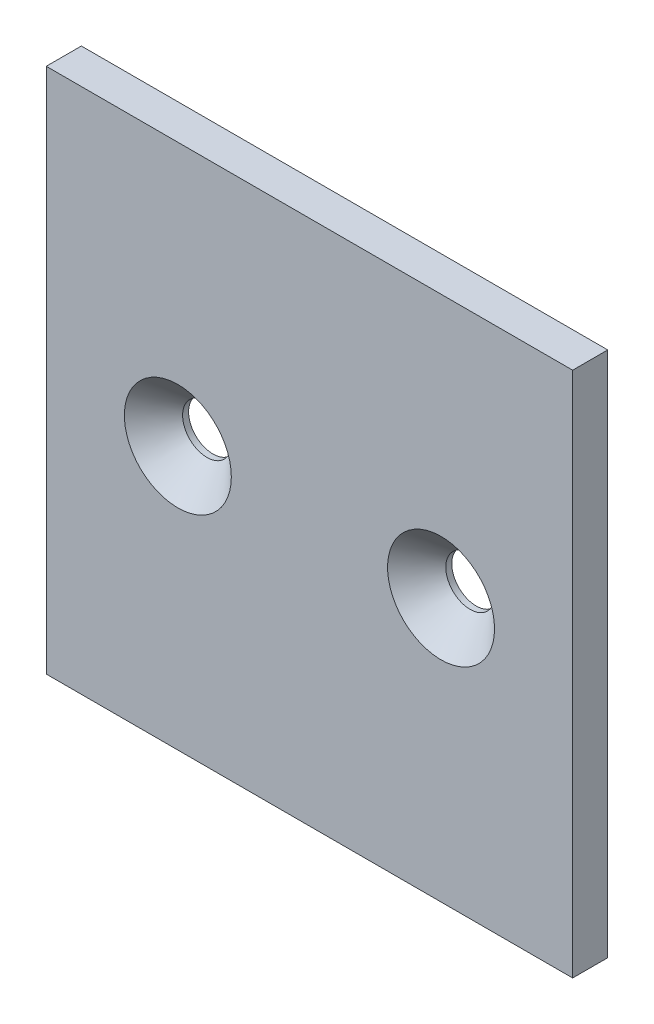
SolidWorks part; units mm, degrees
ref_plane "Front Plane" through (0, 0, 0) normal (0, 0, 1) x (1, 0, 0)
ref_plane "Top Plane" through (0, 0, 0) normal (0, 1, 0) x (1, 0, 0)
ref_plane "Right Plane" through (0, 0, 0) normal (1, 0, 0) x (0, 0, -1)
sketch "Sketch1" plane through (0, 0, 0) normal (0, 0, 1) x (1, 0, 0)
  line L0 (0, 0) -> (0, 90)
  line L1 (22.5, 45) -> (67.5, 45) construction
  line L4 (90, 90) -> (0, 90)
  line L5 (90, 0) -> (0, 0)
  line L7 (90, 90) -> (90, 0)
  circle A0 centre (22.5, 45) radius 4.1656
  circle A1 centre (67.5, 45) radius 4.1656
  dimension "D1" = 45
  dimension "E" = 8.3312
  dimension "D2" = 22.5
  dimension "C" = 90
  dimension "D3" = 45
  dimension "B" = 90
extrude "Boss-Extrude1" add sketch "Sketch1" along normal mid plane 6
sketch "Sketch2" plane through (0, 0, 3) normal (0, 0, 1) x (1, 0, 0)
  circle A1 centre (22.5, 45) radius 9.144
  circle A3 centre (67.5, 45) radius 9.144
  dimension "CSK" = 18.288
extrude "Cut-Extrude1" cut sketch "Sketch2" against normal through all draft 45
sketch "Sketch3" plane through (0, 0, 3) normal (0, 0, 1) x (1, 0, 0)
  line L0 (90, 0) -> (90, 90) construction
  line L1 (90, 90) -> (0, 90) construction
  circle A0 centre (70.4, 57.7) radius 3
  dimension "D1" = 6
  dimension "D2" = 19.6
  dimension "D3" = 32.3
